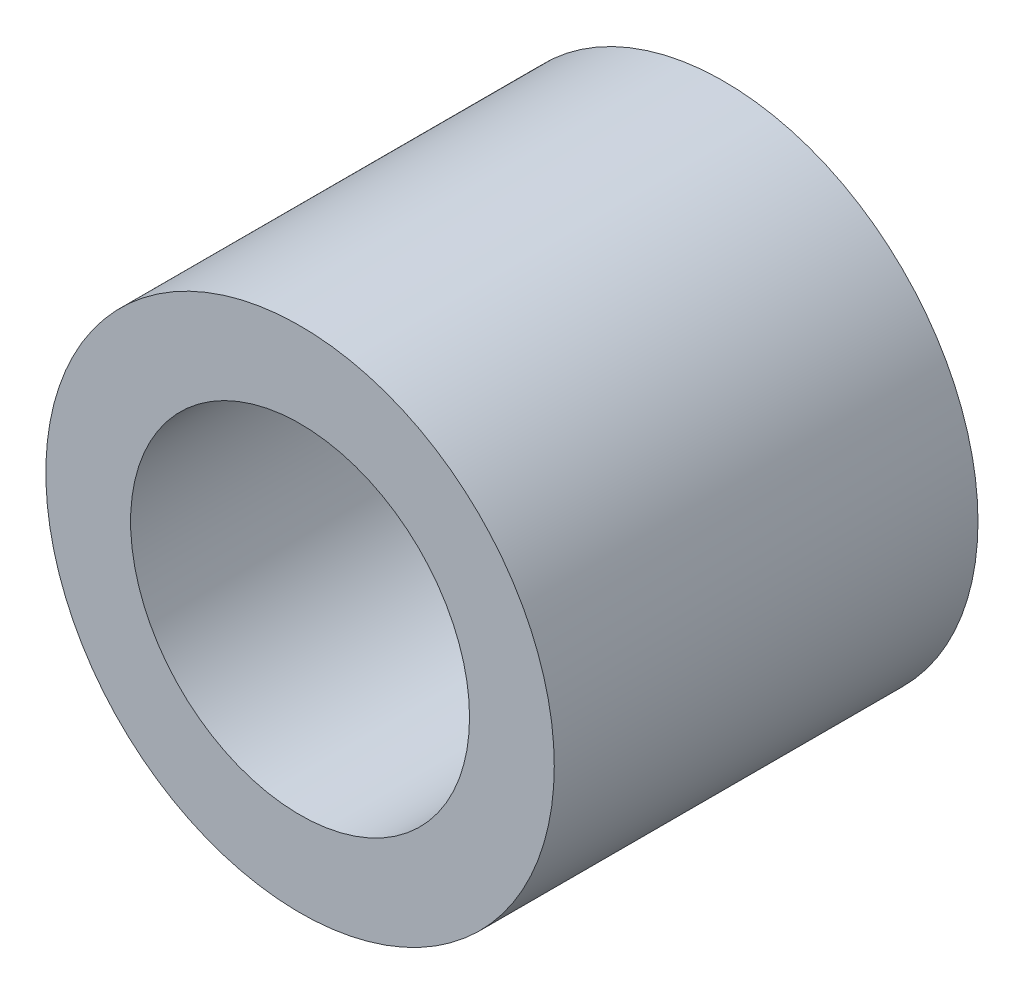
SolidWorks part; units mm, degrees
ref_plane "Plan de face" through (0, 0, 0) normal (0, 0, 1) x (1, 0, 0)
ref_plane "Plan de dessus" through (0, 0, 0) normal (0, 1, 0) x (1, 0, 0)
ref_plane "Plan de droite" through (0, 0, 0) normal (1, 0, 0) x (0, 0, -1)
sketch "Esquisse1" plane through (0, 0, 0) normal (0, 0, 1) x (1, 0, 0)
  circle A0 centre (14.4914, -8.8482) radius 4
  circle A1 centre (14.4914, -8.8482) radius 6
  dimension "D1" = 12
  dimension "D2" = 8
extrude "Boss.-Extru.1" add sketch "Esquisse1" along normal blind 10
